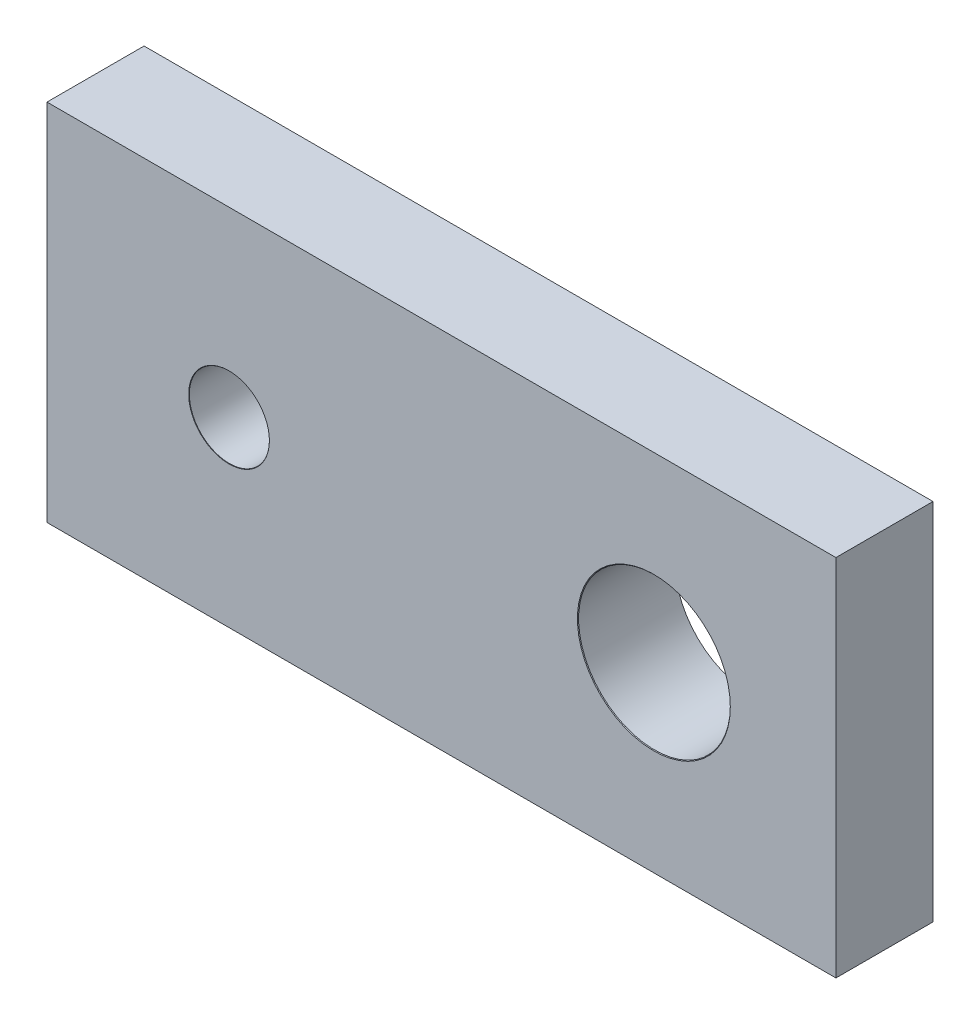
SolidWorks part; units mm, degrees
ref_plane "前视基准面" through (0, 0, 0) normal (0, 0, 1) x (1, 0, 0)
ref_plane "上视基准面" through (0, 0, 0) normal (0, 1, 0) x (1, 0, 0)
ref_plane "右视基准面" through (0, 0, 0) normal (1, 0, 0) x (0, 0, -1)
sketch "草图1" plane through (0, 0, 0) normal (0, 0, 1) x (1, 0, 0)
  line L1 (-32.5, 15) -> (32.5, 15)
  line L2 (-32.5, 15) -> (-32.5, -15)
  line L3 (-32.5, -15) -> (32.5, -15)
  line L4 (32.5, 15) -> (32.5, -15)
  line L5 (-32.5, 15) -> (32.5, -15) construction
  line L6 (-32.5, -15) -> (32.5, 15) construction
  point P0 (0, 0)
  dimension "D1" = 65
  dimension "D2" = 30
extrude "凸台-拉伸1" add sketch "草图1" along normal blind 8
sketch "草图2" plane through (0, 0, 8) normal (0, 0, 1) x (1, 0, 0)
  line L0 (-17.5, 0) -> (17.5, 0)
  line L1 (-32.5, 15) -> (-32.5, -15) construction
  dimension "D1" = 35
  dimension "D2" = 15
hole_wizard "M6 间隙槽口1" positions "草图3" profile "草图4" size "M6" standard "GB" slot yes
sketch "草图3" plane through (0, 0, 8) normal (0, 0, 1) x (1, 0, 0)
  point P0 (-17.5, 0)
sketch "草图4" plane through (-17.5, 0, 8) normal (1, 0, 0) x (0, -1, 0)
  line L0 (0, 0) -> (0, 21.9828)
  line L1 (0, 21.9828) -> (3.3, 20)
  line L2 (3.3, 20) -> (3.3, 0.025)
  line L3 (3.3, 0.025) -> (3.325, 0)
  line L5 (3.325, 0) -> (0, 0)
  line L6 (-3.3, 0.025) -> (-3.325, 0) construction
  line L10 (0, 21.9828) -> (-3.3, 20) construction
  line L11 (0, -6.35) -> (0, 107.95) construction
  dimension "孔直径" = 6.6
  dimension "孔深度" = 20
  dimension "近端锥形沉头孔直径" = 6.65
  dimension "近端锥形沉头孔角度" = 90
  dimension "导头角度" = 118
hole_wizard "M6 间隙槽口2" positions "草图5" profile "草图6" size "M6" standard "GB" slot yes
sketch "草图5" plane through (0, 0, 8) normal (0, 0, 1) x (1, 0, 0)
  point P0 (17.5, 0)
sketch "草图6" plane through (17.5, 0, 8) normal (1, 0, 0) x (0, -1, 0)
  line L0 (0, 0) -> (0, 23.7554)
  line L1 (0, 23.7554) -> (6.25, 20)
  line L2 (6.25, 20) -> (6.25, 0.05)
  line L3 (6.25, 0.05) -> (6.3, 0)
  line L5 (6.3, 0) -> (0, 0)
  line L6 (-6.25, 0.05) -> (-6.3, 0) construction
  line L10 (0, 23.7554) -> (-6.25, 20) construction
  line L11 (0, -6.35) -> (0, 107.95) construction
  dimension "孔直径" = 12.5
  dimension "孔深度" = 20
  dimension "近端锥形沉头孔直径" = 12.6
  dimension "近端锥形沉头孔角度" = 90
  dimension "导头角度" = 118
